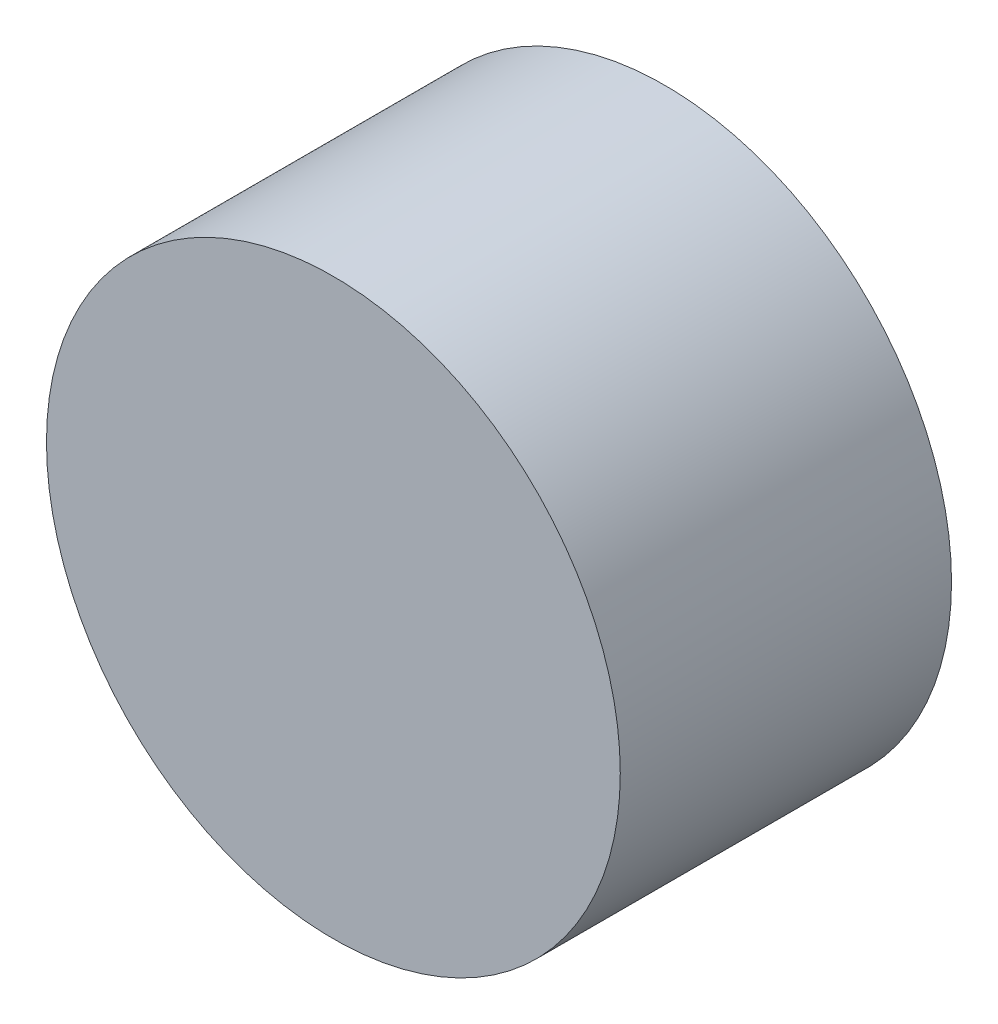
SolidWorks part; units mm, degrees
material "Acrylic (Medium-high impact)"
ref_plane "Front Plane" through (0, 0, 0) normal (0, 0, 1) x (1, 0, 0)
ref_plane "Top Plane" through (0, 0, 0) normal (0, 1, 0) x (1, 0, 0)
ref_plane "Right Plane" through (0, 0, 0) normal (1, 0, 0) x (0, 0, -1)
sketch "Sketch1" plane through (0, 0, 0) normal (0, 0, 1) x (1, 0, 0)
  arc A1 (-2.5, 4.899) -> (2.5, 4.899) centre (0, 0) ccw
  arc A2 (-2.5, 4.899) -> (2.5, 4.899) centre (0, 0) cw
  dimension "D2" = 11
extrude "Boss-Extrude2" add sketch "Sketch1" along normal blind 6.35
